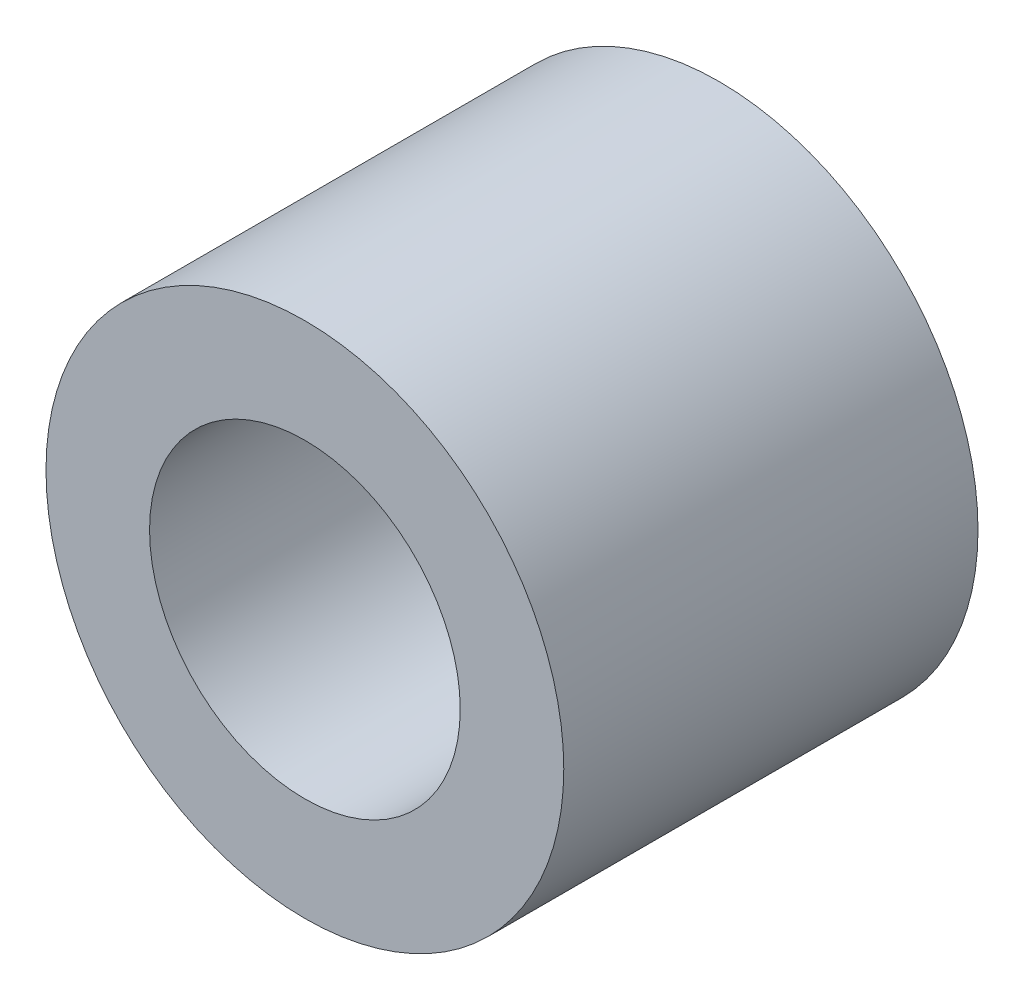
SolidWorks part; units mm, degrees
ref_plane "Front Plane" through (0, 0, 0) normal (0, 0, 1) x (1, 0, 0)
ref_plane "Top Plane" through (0, 0, 0) normal (0, 1, 0) x (1, 0, 0)
ref_plane "Right Plane" through (0, 0, 0) normal (1, 0, 0) x (0, 0, -1)
sketch "Sketch1" plane through (0, 0, 0) normal (0, 0, 1) x (1, 0, 0)
  circle A0 centre (0, 0) radius 3.9688
  circle A1 centre (0, 0) radius 2.3812
  dimension "D1" = 7.9375
  dimension "ID" = 4.7625
extrude "Extrude1" add sketch "Sketch1" along normal mid plane 6.35
sketch "Sketch2" plane through (0, 0, 0) normal (1, 0, 0) x (0, 0, -1)
  line L0 (-3.175, -2.3812) -> (3.175, -2.3812) construction
  line L3 (3.175, 2.3812) -> (-3.175, 2.3812) construction
  line L5 (-3.175, -2.3812) -> (3.175, -2.3812)
  line L6 (3.175, 2.3812) -> (-3.175, 2.3812)
sketch "Sketch4" plane through (0, 0, 3.175) normal (0, 0, 1) x (1, 0, 0)
  line L0 (0, 0) -> (-1.6838, 1.6838)
  line L1 (0, -3.4925) -> (0, 3.4925) construction
  circle A0 centre (0, 0) radius 2.3812 construction
  dimension "D1" = 45
